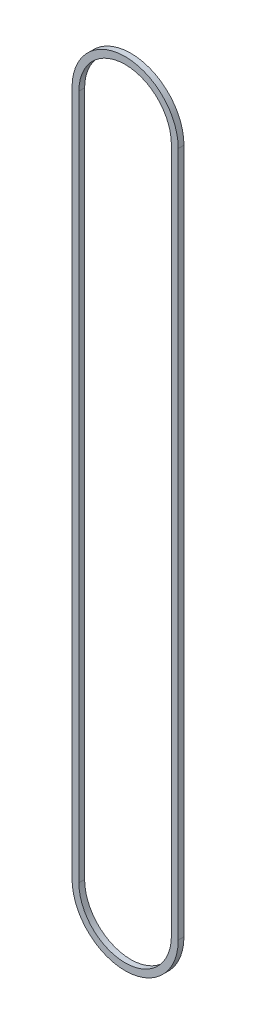
SolidWorks part; units mm, degrees
ref_plane "Front Plane" through (0, 0, 0) normal (0, 0, 1) x (1, 0, 0)
ref_plane "Top Plane" through (0, 0, 0) normal (0, 1, 0) x (1, 0, 0)
ref_plane "Right Plane" through (0, 0, 0) normal (1, 0, 0) x (0, 0, -1)
sketch "Sketch1" plane through (0, 0, 0) normal (0, 0, 1) x (1, 0, 0)
  line L0 (0, 0) -> (0, 762) construction
  line L1 (-51.3969, 0) -> (-51.3969, 762)
  line L2 (51.3969, 0) -> (51.3969, 762)
  line L3 (-59.0169, 0) -> (-59.0169, 762)
  line L4 (59.0169, 0) -> (59.0169, 762)
  arc A0 (-51.3969, 0) -> (51.3969, 0) centre (0, 0) ccw
  arc A1 (51.3969, 762) -> (-51.3969, 762) centre (0, 762) ccw
  arc A2 (59.0169, 762) -> (-59.0169, 762) centre (0, 762) ccw
  arc A3 (-59.0169, 0) -> (59.0169, 0) centre (0, 0) ccw
  point P3 (0, 381)
  dimension "D1" = 51.3969
  dimension "D2" = 762
  dimension "D3" = 7.62
extrude "Boss-Extrude1" add sketch "Sketch1" along normal blind 6.35
